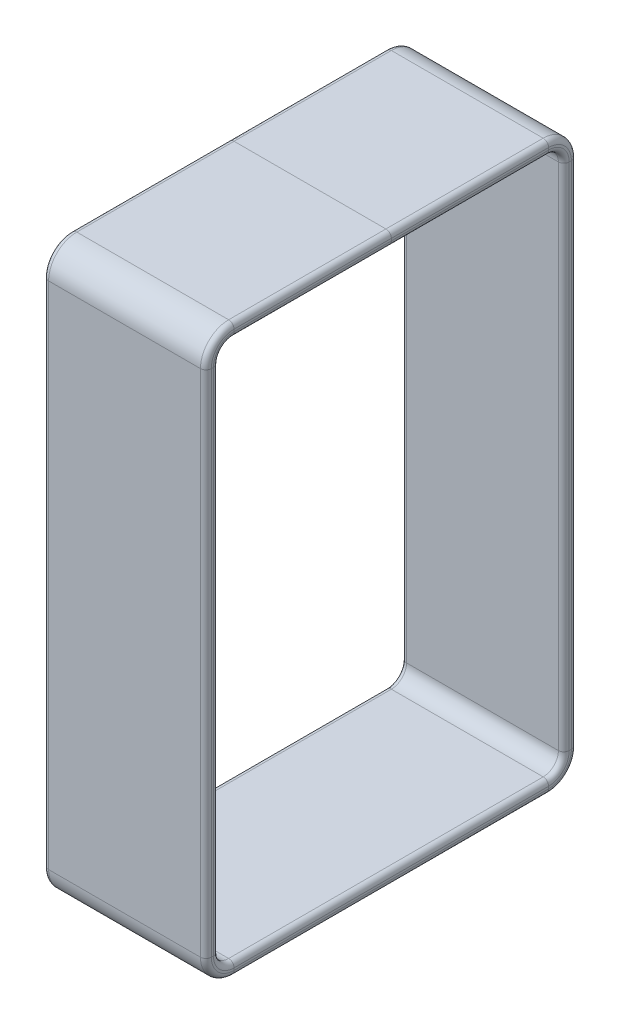
SolidWorks part; units mm, degrees
ref_plane "Front Plane" through (0, 0, 0) normal (0, 0, 1) x (1, 0, 0)
ref_plane "Top Plane" through (0, 0, 0) normal (0, 1, 0) x (1, 0, 0)
ref_plane "Right Plane" through (0, 0, 0) normal (1, 0, 0) x (0, 0, -1)
sketch "Sketch1" plane through (0, 0, 0) normal (1, 0, 0) x (0, 0, -1)
  line L1 (14.5, 25.5) -> (-14.5, 25.5)
  line L2 (16.5, 23.5) -> (16.5, -23.5)
  line L3 (14.5, -25.5) -> (-14.5, -25.5)
  line L4 (-16.5, 23.5) -> (-16.5, -23.5)
  line L5 (16.5, 25.5) -> (-16.5, -25.5) construction
  line L6 (16.5, -25.5) -> (-16.5, 25.5) construction
  arc A0 (-14.5, -25.5) -> (-16.5, -23.5) centre (-14.5, -23.5) cw
  arc A1 (16.5, -23.5) -> (14.5, -25.5) centre (14.5, -23.5) cw
  arc A2 (14.5, 25.5) -> (16.5, 23.5) centre (14.5, 23.5) cw
  arc A3 (-14.5, 25.5) -> (-16.5, 23.5) centre (-14.5, 23.5) ccw
  point P0 (0, 0)
  dimension "D3" = 2
  dimension "D1" = 51
  dimension "D2" = 33
sketch "Sketch2" plane through (0, 0, 0) normal (0, 0, 1) x (1, 0, 0)
  line L0 (0, -25.5) -> (0, 25.5) construction
  line L1 (-7, 26.1) -> (7, 26.1)
  line L2 (-7.5, 25.6) -> (-7.5, 25.4)
  line L3 (-7, 24.9) -> (7, 24.9)
  line L4 (7.5, 25.6) -> (7.5, 25.4)
  line L5 (-7.5, 26.1) -> (7.5, 24.9) construction
  line L6 (-7.5, 24.9) -> (7.5, 26.1) construction
  line L7 (0, 25.5) -> (0, -25.5) construction
  arc A0 (7, 24.9) -> (7.5, 25.4) centre (7, 25.4) ccw
  arc A1 (7, 26.1) -> (7.5, 25.6) centre (7, 25.6) cw
  arc A2 (-7.5, 25.4) -> (-7, 24.9) centre (-7, 25.4) ccw
  arc A3 (-7, 26.1) -> (-7.5, 25.6) centre (-7, 25.6) ccw
  point P0 (0, 25.5)
  point P7 (0, 24.5)
  point P8 (0, 26.5)
  point P9 (0, 25.5)
  dimension "D3" = 0.5
  dimension "D1" = 15
  dimension "D2" = 1.2
sweep "Sweep1" add profiles "Sketch2" path "Sketch1"
